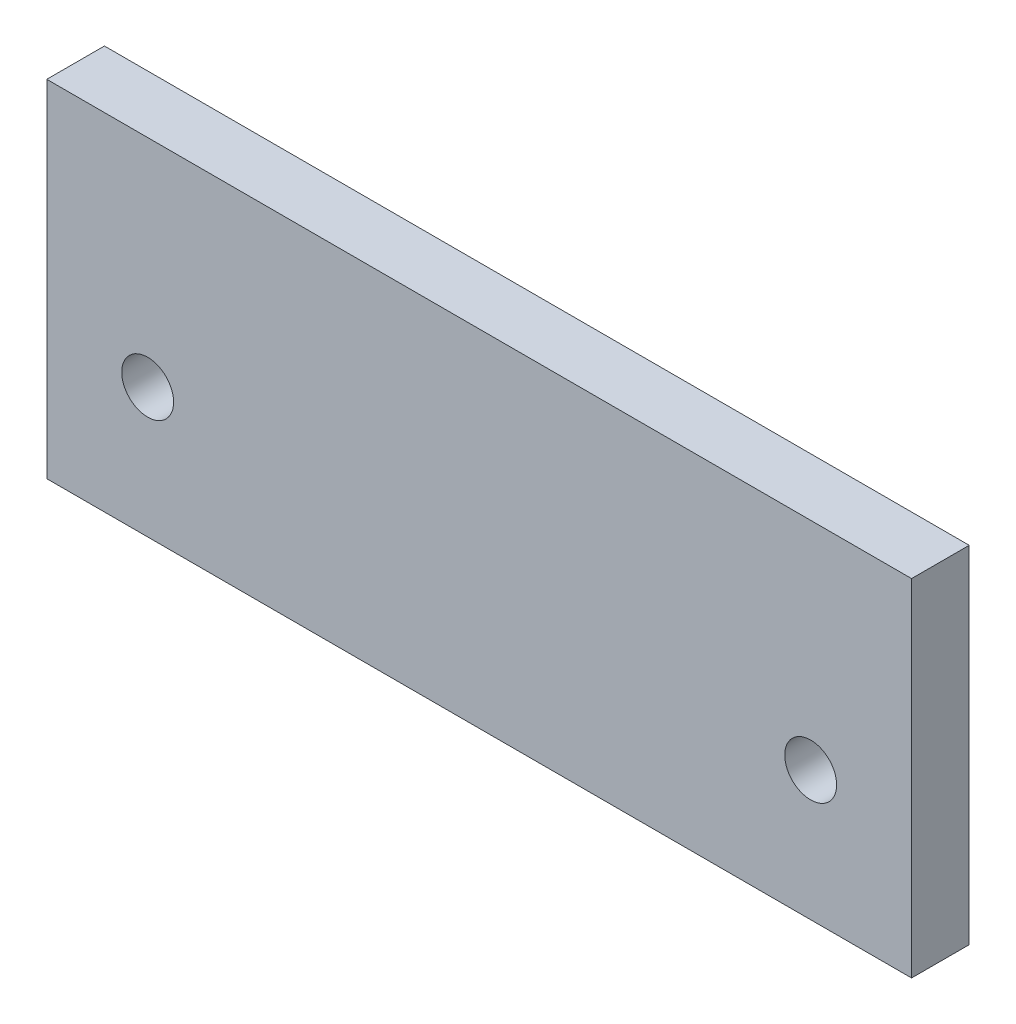
SolidWorks part; units mm, degrees
material "Plain Carbon Steel"
ref_plane "Front Plane" through (0, 0, 0) normal (0, 0, 1) x (1, 0, 0)
ref_plane "Top Plane" through (0, 0, 0) normal (0, 1, 0) x (1, 0, 0)
ref_plane "Right Plane" through (0, 0, 0) normal (1, 0, 0) x (0, 0, -1)
sketch "Sketch1" plane through (0, 0, 0) normal (0, 0, 1) x (1, 0, 0)
  line L1 (0, 0) -> (300, 0)
  line L2 (0, 0) -> (0, 120)
  line L3 (0, 120) -> (300, 120)
  line L4 (300, 0) -> (300, 120)
  dimension "D1" = 300
  dimension "D2" = 120
extrude "Boss-Extrude1" add sketch "Sketch1" along normal blind 20
sketch "Sketch2" plane through (0, 0, 20) normal (0, 0, 1) x (1, 0, 0)
  line L0 (253, 45) -> (277, 45) construction
  line L1 (23, 45) -> (47, 45) construction
  arc A0 (262, 54) -> (262, 36) centre (262, 45) ccw construction
  arc A1 (268, 36) -> (268, 54) centre (268, 45) ccw construction
  arc A2 (32, 54) -> (32, 36) centre (32, 45) ccw construction
  arc A3 (38, 36) -> (38, 54) centre (38, 45) ccw construction
  circle A4 centre (265, 45) radius 9
  circle A5 centre (35, 45) radius 9
extrude "Cut-Extrude1" cut sketch "Sketch2" against normal through all
sketch "Sketch3" [suppressed] plane through (300, 0, 0) normal (1, 0, 0) x (0, 0, -1)
  line L0 (-20, 10) -> (-10, 0)
  line L1 (-20, 0) -> (-20, 95) construction
  line L2 (-20, 0) -> (0, 0) construction
  line L3 (-10, 0) -> (0, 10)
  line L4 (0, 0) -> (0, 95) construction
  dimension "D1" = 45
extrude "Cut-Extrude2" [suppressed] cut sketch "Sketch3" against normal through all and the other way through all flip side to cut
sketch "Sketch4" plane through (0, 0, 20) normal (0, 0, 1) x (1, 0, 0)
  circle A0 centre (35, 45) radius 9 construction
  point P0 (265, 45)
  point P1 (42.5977, 49.8244)
  point P3 (35, 45)
